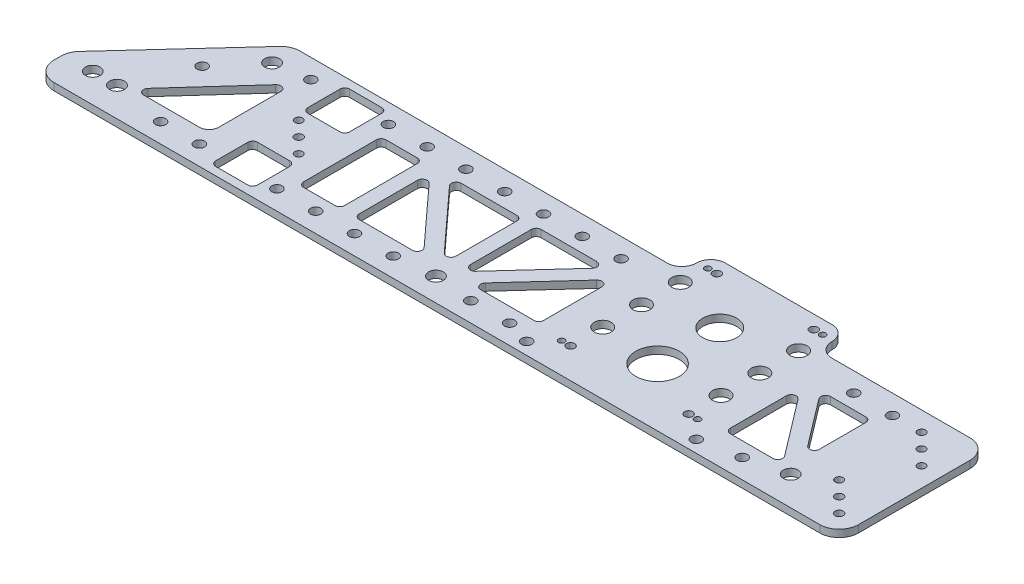
SolidWorks part; units mm, degrees
ref_plane "Front Plane" through (0, 0, 0) normal (0, 0, 1) x (1, 0, 0)
ref_plane "Top Plane" through (0, 0, 0) normal (0, 1, 0) x (1, 0, 0)
ref_plane "Right Plane" through (0, 0, 0) normal (1, 0, 0) x (0, 0, -1)
ref_plane "Plane1" through (0, 0, 0) normal (0, -1, 0) x (1, 0, 0)
sketch "Sketch1" plane through (0, 0, 0) normal (0, -1, 0) x (1, 0, 0)
  line L0 (335.0692, -117.475) -> (404.9192, -117.475)
  line L1 (423.9692, -98.425) -> (514.35, -98.425)
  line L2 (527.05, -85.725) -> (527.05, -12.7)
  line L3 (514.35, 0) -> (12.7, 0)
  line L4 (0, -12.7) -> (0, -17.2849)
  line L5 (3.3381, -25.8666) -> (66.0749, -94.3067)
  line L6 (75.4368, -98.425) -> (316.0192, -98.425)
  line L7 (137.541, -68.834) -> (137.541, -89.916)
  line L8 (134.366, -93.091) -> (113.284, -93.091)
  line L9 (110.109, -89.916) -> (110.109, -68.834)
  line L10 (113.284, -65.659) -> (134.366, -65.659)
  line L11 (137.541, -8.509) -> (137.541, -29.591)
  line L12 (134.366, -32.766) -> (113.284, -32.766)
  line L13 (110.109, -29.591) -> (110.109, -8.509)
  line L14 (113.284, -5.334) -> (134.366, -5.334)
  line L15 (86.5456, -71.372) -> (46.8792, -27.5301)
  line L16 (49.2335, -22.225) -> (85.725, -22.225)
  line L17 (92.075, -28.575) -> (92.075, -69.2419)
  line L18 (463.9807, -27.3213) -> (436.0346, -64.087)
  line L19 (430.3319, -62.1657) -> (430.3319, -25.4)
  line L20 (433.5069, -22.225) -> (461.453, -22.225)
  line L21 (292.0517, -76.2) -> (255.5875, -76.2)
  line L22 (252.4125, -73.025) -> (252.4125, -33.1442)
  line L23 (257.9307, -31.0017) -> (294.3949, -70.8826)
  line L24 (270.0172, -22.225) -> (304.894, -22.225)
  line L25 (308.069, -25.4) -> (308.069, -63.5446)
  line L26 (302.5508, -65.687) -> (267.674, -27.5424)
  line L27 (239.7125, -76.2) -> (203.2483, -76.2)
  line L28 (200.9051, -70.8826) -> (237.3693, -31.0017)
  line L29 (242.8875, -33.1442) -> (242.8875, -73.025)
  line L30 (190.406, -22.225) -> (225.2828, -22.225)
  line L31 (227.626, -27.5424) -> (192.7492, -65.687)
  line L32 (187.231, -63.5446) -> (187.231, -25.4)
  line L33 (177.706, -25.4) -> (177.706, -73.025)
  line L34 (174.531, -76.2) -> (153.9875, -76.2)
  line L35 (150.8125, -73.025) -> (150.8125, -25.4)
  line L36 (153.9875, -22.225) -> (174.531, -22.225)
  line L37 (471.4875, -42.6093) -> (471.4875, -73.025)
  line L38 (468.3125, -76.2) -> (445.1931, -76.2)
  line L39 (442.6654, -71.1037) -> (465.7848, -40.688)
  circle A0 centre (34.925, -19.05) radius 4.826
  circle A1 centre (408.7452, -66.3194) radius 5.5626
  circle A2 centre (331.2432, -40.9194) radius 5.5626
  circle A3 centre (331.2432, -66.3194) radius 5.5626
  circle A4 centre (369.9942, -38.1) radius 14.2812
  circle A5 centre (247.65, -15.24) radius 4.826
  circle A6 centre (19.05, -19.05) radius 4.826
  circle A7 centre (476.25, -19.05) radius 4.826
  circle A8 centre (369.9942, -78.8162) radius 11.1061
  circle A9 centre (331.2432, -91.7194) radius 5.5626
  circle A10 centre (408.7452, -91.7194) radius 5.5626
  circle A11 centre (408.7452, -40.9194) radius 5.5626
  circle A12 centre (314.419, -7.9248) radius 3.3782
  circle A13 centre (338.2442, -108.6612) radius 2.667
  circle A14 centre (425.5694, -7.9248) radius 3.3782
  circle A15 centre (401.7442, -108.6612) radius 2.667
  circle A16 centre (331.3354, -19.7866) radius 2.667
  circle A17 centre (408.653, -19.7866) radius 2.667
  circle A18 centre (332.4022, -108.6612) radius 2.032
  circle A19 centre (325.4934, -19.7866) radius 2.032
  circle A20 centre (407.5862, -108.6612) radius 2.032
  circle A21 centre (414.495, -19.7866) radius 2.032
  arc A22 (316.0192, -98.425) -> (325.5442, -107.95) centre (316.0192, -107.95) cw
  arc A23 (325.5442, -107.95) -> (335.0692, -117.475) centre (335.0692, -107.95) ccw
  arc A24 (404.9192, -117.475) -> (414.4442, -107.95) centre (404.9192, -107.95) ccw
  arc A25 (414.4442, -107.95) -> (423.9692, -98.425) centre (423.9692, -107.95) cw
  arc A26 (514.35, -98.425) -> (527.05, -85.725) centre (514.35, -85.725) ccw
  arc A27 (527.05, -12.7) -> (514.35, 0) centre (514.35, -12.7) ccw
  arc A28 (12.7, 0) -> (0, -12.7) centre (12.7, -12.7) ccw
  arc A29 (0, -17.2849) -> (3.3381, -25.8666) centre (12.7, -17.2849) ccw
  arc A30 (66.0749, -94.3067) -> (75.4368, -98.425) centre (75.4368, -85.725) ccw
  circle A31 centre (73.025, -82.55) radius 4.826
  circle A32 centre (95.25, -12.7) radius 3.3782
  circle A33 centre (95.25, -85.725) radius 3.3782
  circle A34 centre (146.05, -12.7) radius 3.3782
  circle A35 centre (146.05, -85.725) radius 3.3782
  circle A36 centre (171.45, -12.7) radius 3.3782
  circle A37 centre (171.45, -85.725) radius 3.3782
  circle A38 centre (196.85, -12.7) radius 3.3782
  circle A39 centre (196.85, -85.725) radius 3.3782
  circle A40 centre (222.25, -12.7) radius 3.3782
  circle A41 centre (222.25, -85.725) radius 3.3782
  circle A42 centre (247.65, -85.725) radius 3.3782
  circle A43 centre (273.05, -12.7) radius 3.3782
  circle A44 centre (273.05, -85.725) radius 3.3782
  circle A45 centre (298.45, -12.7) radius 3.3782
  circle A46 centre (298.45, -85.725) radius 3.3782
  circle A47 centre (450.85, -12.7) radius 3.3782
  circle A48 centre (476.25, -85.725) radius 3.3782
  arc A49 (137.541, -89.916) -> (134.366, -93.091) centre (134.366, -89.916) cw
  arc A50 (113.284, -93.091) -> (110.109, -89.916) centre (113.284, -89.916) cw
  arc A51 (110.109, -68.834) -> (113.284, -65.659) centre (113.284, -68.834) cw
  arc A52 (134.366, -65.659) -> (137.541, -68.834) centre (134.366, -68.834) cw
  arc A53 (137.541, -29.591) -> (134.366, -32.766) centre (134.366, -29.591) cw
  arc A54 (113.284, -32.766) -> (110.109, -29.591) centre (113.284, -29.591) cw
  arc A55 (110.109, -8.509) -> (113.284, -5.334) centre (113.284, -8.509) cw
  arc A56 (134.366, -5.334) -> (137.541, -8.509) centre (134.366, -8.509) cw
  circle A57 centre (450.85, -85.725) radius 3.3782
  arc A58 (92.075, -69.2419) -> (86.5456, -71.372) centre (88.9, -69.2419) cw
  arc A59 (46.8792, -27.5301) -> (49.2335, -22.225) centre (49.2335, -25.4) cw
  arc A60 (85.725, -22.225) -> (92.075, -28.575) centre (85.725, -28.575) cw
  arc A61 (461.453, -22.225) -> (463.9807, -27.3213) centre (461.453, -25.4) cw
  arc A62 (436.0346, -64.087) -> (430.3319, -62.1657) centre (433.5069, -62.1657) cw
  arc A63 (430.3319, -25.4) -> (433.5069, -22.225) centre (433.5069, -25.4) cw
  arc A64 (294.3949, -70.8826) -> (292.0517, -76.2) centre (292.0517, -73.025) cw
  arc A65 (255.5875, -76.2) -> (252.4125, -73.025) centre (255.5875, -73.025) cw
  arc A66 (252.4125, -33.1442) -> (257.9307, -31.0017) centre (255.5875, -33.1442) cw
  arc A67 (267.674, -27.5424) -> (270.0172, -22.225) centre (270.0172, -25.4) cw
  arc A68 (304.894, -22.225) -> (308.069, -25.4) centre (304.894, -25.4) cw
  arc A69 (308.069, -63.5446) -> (302.5508, -65.687) centre (304.894, -63.5446) cw
  arc A70 (242.8875, -73.025) -> (239.7125, -76.2) centre (239.7125, -73.025) cw
  arc A71 (203.2483, -76.2) -> (200.9051, -70.8826) centre (203.2483, -73.025) cw
  arc A72 (237.3693, -31.0017) -> (242.8875, -33.1442) centre (239.7125, -33.1442) cw
  arc A73 (187.231, -25.4) -> (190.406, -22.225) centre (190.406, -25.4) cw
  arc A74 (225.2828, -22.225) -> (227.626, -27.5424) centre (225.2828, -25.4) cw
  arc A75 (192.7492, -65.687) -> (187.231, -63.5446) centre (190.406, -63.5446) cw
  arc A76 (174.531, -22.225) -> (177.706, -25.4) centre (174.531, -25.4) cw
  arc A77 (177.706, -73.025) -> (174.531, -76.2) centre (174.531, -73.025) cw
  arc A78 (153.9875, -76.2) -> (150.8125, -73.025) centre (153.9875, -73.025) cw
  arc A79 (150.8125, -25.4) -> (153.9875, -22.225) centre (153.9875, -25.4) cw
  arc A80 (465.7848, -40.688) -> (471.4875, -42.6093) centre (468.3125, -42.6093) cw
  arc A81 (471.4875, -73.025) -> (468.3125, -76.2) centre (468.3125, -73.025) cw
  arc A82 (445.1931, -76.2) -> (442.6654, -71.1037) centre (445.1931, -73.025) cw
  circle A83 centre (495.3, -85.725) radius 2.5527
  circle A84 centre (504.825, -76.2) radius 2.5527
  circle A85 centre (514.35, -66.675) radius 2.5527
  circle A86 centre (504.825, -22.225) radius 2.667
  circle A87 centre (495.3, -31.75) radius 2.5527
  circle A88 centre (514.35, -12.7) radius 2.667
  circle A89 centre (123.825, -49.2125) radius 2.667
  circle A90 centre (133.35, -39.6875) radius 2.5527
  circle A91 centre (114.3, -58.7375) radius 2.5527
  circle A92 centre (69.85, -12.7) radius 3.3782
  circle A93 centre (51.9505, -57.7565) radius 3.3782
extrude "Boss-Extrude1" add sketch "Sketch1" against normal blind 4.7625
